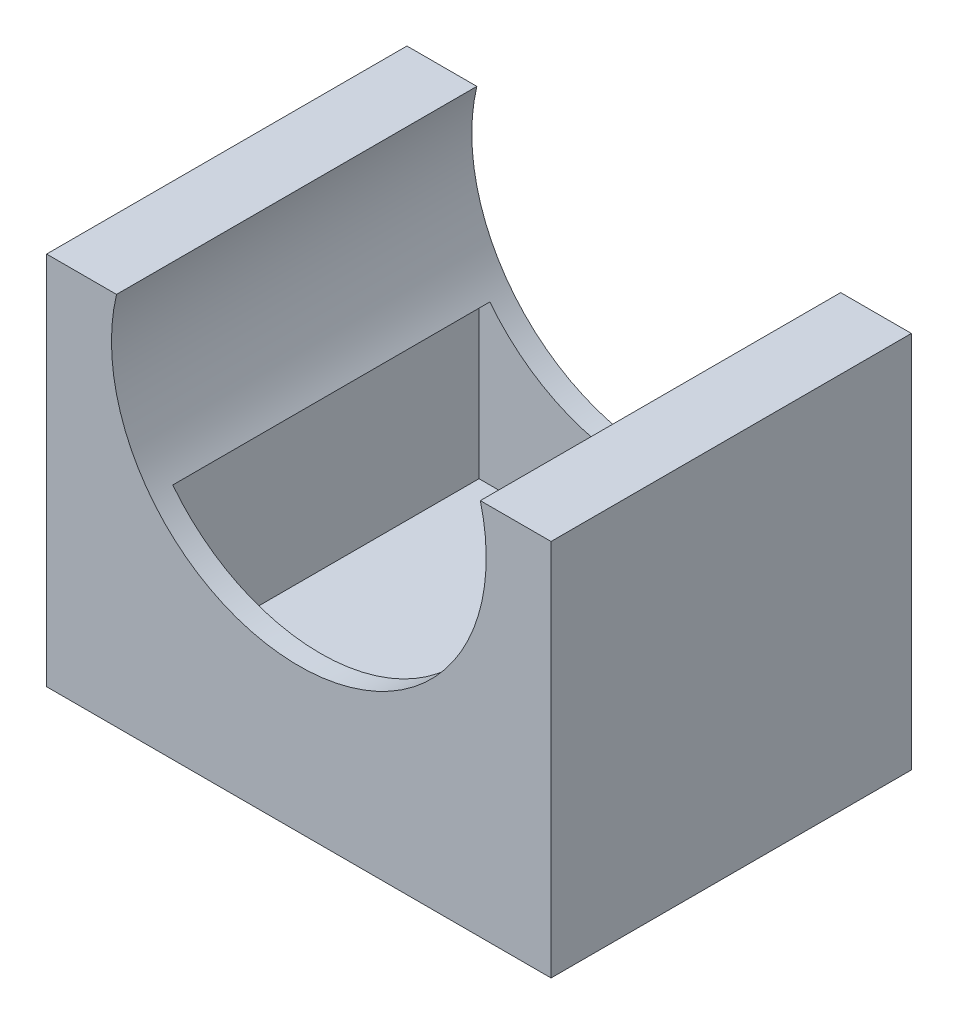
SolidWorks part; units mm, degrees
ref_plane "Front Plane" through (0, 0, 0) normal (0, 0, 1) x (1, 0, 0)
ref_plane "Top Plane" through (0, 0, 0) normal (0, 1, 0) x (1, 0, 0)
ref_plane "Right Plane" through (0, 0, 0) normal (1, 0, 0) x (0, 0, -1)
sketch "Sketch1" plane through (0, 0, 0) normal (0, 0, 1) x (1, 0, 0)
  line L0 (0, 0) -> (70, 0)
  line L1 (0, 0) -> (0, 10)
  line L2 (0, 10) -> (70, 10)
  line L3 (70, 10) -> (70, 0)
  line L4 (35, 0) -> (35, 40) construction
  line L5 (35, 40) -> (9.7018, 46) construction
  line L6 (35, 40) -> (60.1849, 46.4592) construction
  line L7 (9.7018, 46) -> (0, 46)
  line L8 (0, 46) -> (0, 10)
  line L9 (60.1849, 46.4592) -> (70, 46.4592)
  line L10 (70, 46.4592) -> (70, 10)
  arc A0 (60.1849, 46.4592) -> (9.7018, 46) centre (35, 40) cw
  point P10 (0, 0)
  point P13 (0, 0)
  dimension "D4" = 26
  dimension "D1" = 70
  dimension "D2" = 10
  dimension "D3" = 40
  dimension "D5" = 6
  dimension "D6" = 26
  dimension "D7" = 50.4831
extrude "Boss-Extrude2" add sketch "Sketch1" along normal blind 50 contours L9 A0 L7 L8 L2 L10 | L3 L2 L1 L0
ref_plane "Plane1" through (0, 14, 0) normal (0, 1, 0) x (1, 0, 0)
sketch "Sketch2" plane through (0, 14, 0) normal (0, 1, 0) x (1, 0, 0)
  line L0 (35, -50) -> (35, 0) construction
  line L1 (9, -50) -> (61, -50) construction
  line L2 (61, 0) -> (9, 0) construction
  line L4 (57, -47) -> (13, -47)
  line L5 (57, -47) -> (57, -3)
  line L6 (57, -3) -> (13, -3)
  line L7 (13, -47) -> (13, -3)
  line L8 (57, -47) -> (13, -3) construction
  line L9 (57, -3) -> (13, -47) construction
  point P6 (35, -25)
  dimension "D1" = 44
  dimension "D2" = 44
extrude "Cut-Extrude6" cut sketch "Sketch2" along normal blind 10
sketch "Sketch3" plane through (0, 14, 0) normal (0, 1, 0) x (1, 0, 0)
  line L1 (13, -3) -> (57, -3)
  line L2 (13, -3) -> (13, -47)
  line L3 (13, -47) -> (57, -47)
  line L4 (57, -3) -> (57, -47)
extrude "Cut-Extrude8" cut sketch "Sketch3" against normal blind 12
sketch "Sketch6" plane through (0, 0, 0) normal (0, 0, 1) x (1, 0, 0)
  line L1 (0, 0) -> (70, 0)
  line L2 (0, 0) -> (0, -6)
  line L3 (0, -6) -> (70, -6)
  line L4 (70, 0) -> (70, -6)
  dimension "D1" = 6
extrude "Boss-Extrude3" add sketch "Sketch6" along normal blind 50
